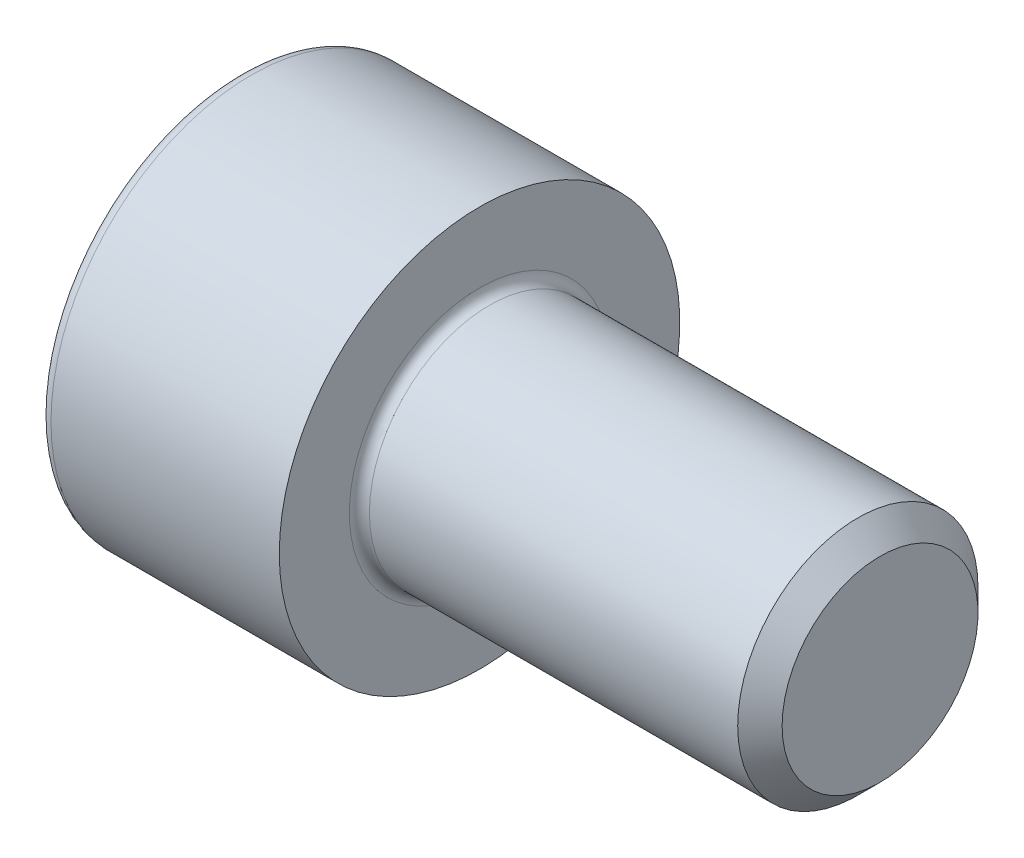
SolidWorks part; units mm, degrees
ref_plane "Plane1" through (0, 0, 0) normal (0, 0, 1) x (1, 0, 0)
ref_plane "Plane2" through (0, 0, 0) normal (0, 1, 0) x (1, 0, 0)
ref_plane "Plane3" through (0, 0, 0) normal (1, 0, 0) x (0, 0, -1)
sketch "BodySke" plane through (0, 0, 0) normal (0, 0, 1) x (1, 0, 0)
  line L0 (0, 0) -> (0, 5)
  line L1 (0, 5) -> (6, 5)
  line L2 (6, 5) -> (6, 3)
  line L3 (6, 3) -> (15.4455, 3)
  line L4 (16, 2.4455) -> (16, 0)
  line L5 (16, 0) -> (0, 0)
  line L6 (-31.75, 0) -> (127, 0) construction
  line L8 (16, 2.4455) -> (15.4455, 3)
  line L10 (16, -2.4455) -> (15.4455, -3) construction
  line L11 (5, 9.525) -> (5, 3.175) construction
  line L12 (-4, 9.525) -> (-4, 3.175) construction
  line L13 (-29, 9.525) -> (-29, 3.175) construction
  dimension "Diameter" = 6
  dimension "Head_ht" = 6
  dimension "Length" = 10
  dimension "Body_ch_ang" = 45
  dimension "Head_dia" = 10
  dimension "Minor_dia" = 4.891
  dimension "Advance" = 1
  dimension "Thread_nom" = 20
  dimension "Thread_length" = 45
revolve "Base-Revolve" add sketch "BodySke" angle 360 about L6
cosmetic thread "ThreadCosmetic" parameters "Thread_length"=7, "Thread_minor"=4.891
fillet "Fillet1" radius 0.25 1 edges at (6, 0, 3)
fillet "Fillet2" radius 0.3 1 edges at (0, 0, 5)
sketch "Sketch2" plane through (0, 0, 0) normal (0, 0, 1) x (1, 0, 0)
  line L0 (0, 2.542) -> (3, 2.542)
  line L1 (3, 2.542) -> (4.4676, 0)
  line L2 (-31.75, 0) -> (127, 0) construction
  line L3 (4.4676, 0) -> (0, 0)
  line L4 (0, 0) -> (0, 2.542)
  line L6 (0, 0) -> (47.625, 0) construction
  dimension "D1" = 2.542
  dimension "D2" = 60
  dimension "Depth" = 3
revolve "Hex-PreBroach" cut sketch "Sketch2" angle 360 about L6
sketch "Sketch3" plane through (0, 0, 0) normal (-1, 0, 0) x (0, 0.5, 0.866)
  line L0 (1.4676, 2.542) -> (-1.4676, 2.542)
  line L1 (-1.4676, 2.542) -> (-2.9352, 0)
  line L2 (1.4676, 2.542) -> (2.9352, 0)
  line L3 (1.4676, -2.542) -> (2.9352, 0)
  line L4 (1.4676, -2.542) -> (-1.4676, -2.542)
  line L5 (-1.4676, -2.542) -> (-2.9352, 0)
  dimension "D1" = 2.542
  dimension "D2" = 2.542
  dimension "Hex_size" = 5.084
extrude "Hex" cut sketch "Sketch3" against normal blind 3
sketch "ThdSchSke" plane through (0, 0, 0) normal (0, 0, 1) x (1, 0, 0)
  line L0 (9, -2.4455) -> (8.6117, -3)
  line L1 (9, -2.4455) -> (9.3883, -3)
  line L2 (9.3883, -3) -> (9.3883, -3.75)
  line L3 (-3.175, 0) -> (5.1513, 0) construction
  line L4 (0, 4.7) -> (0, -4.7) construction
  line L5 (9.3883, -3.75) -> (8.6117, -3.75)
  line L6 (8.6117, -3.75) -> (8.6117, -3)
  dimension "Thread_minor" = 4.891
  dimension "Diameter" = 6
  dimension "Start" = 9
  dimension "SideAngle" = 55
  dimension "VeeAngle" = 70
  dimension "Overcut" = 7.5
revolve "ThreadSchematic" [suppressed] cut sketch "ThdSchSke" angle 360 about L3
pattern_linear "ThdSchPat" [suppressed]
equation "\"D2@Sketch3\" = \"Hex_size@Sketch3\" / 2"
equation "\"D1@Sketch3\" = \"Hex_size@Sketch3\" / 2"
equation "\"D1@Sketch2\" = \"Hex_size@Sketch3\" / 2"
equation "\"Thread_minor@ThreadCosmetic\"  =  \"Minor_dia@BodySke\""
equation "\"Depth@Sketch2\" =  \"Key_eng@Hex\""
equation "\"Thread_length@ThreadCosmetic\" = ((sgn( (\"Length@BodySke\" - \"Advance@BodySke\" * 3.0) - \"Thread_nom@BodySke\" )-1)*( (\"Length@BodySke\" - \"Advance@BodySke\" * 3.0) - \"Thread_nom@BodySke\" ))/-2+ \"Thread_nom@BodySke\""
equation "\"Thread_minor@ThdSchSke\" = \"Minor_dia@BodySke\""
equation "\"Diameter@ThdSchSke\" = \"Diameter@BodySke\""
equation "\"Overcut@ThdSchSke\" = \"Diameter@BodySke\" * 1.25"
equation "\"Start@ThdSchSke\" = \"Head_ht@BodySke\" + \"Length@BodySke\" - \"Thread_length@ThreadCosmetic\"  '---Non-countersunk---"
equation "\"Num_threads@ThdSchPat\" = int( \"Thread_length@ThreadCosmetic\" / \"Advance@BodySke\" + 0.999 )  + 1"
equation "\"Advance@ThdSchPat\" = \"Thread_length@ThreadCosmetic\" /  (\"Num_threads@ThdSchPat\" - 1) 'relax it"
equation "\"Num_threads@ThdSchPat\" = \"Num_threads@ThdSchPat\" - sgn( \"Num_threads@ThdSchPat\" - 1) '---chamfered tips only---"
